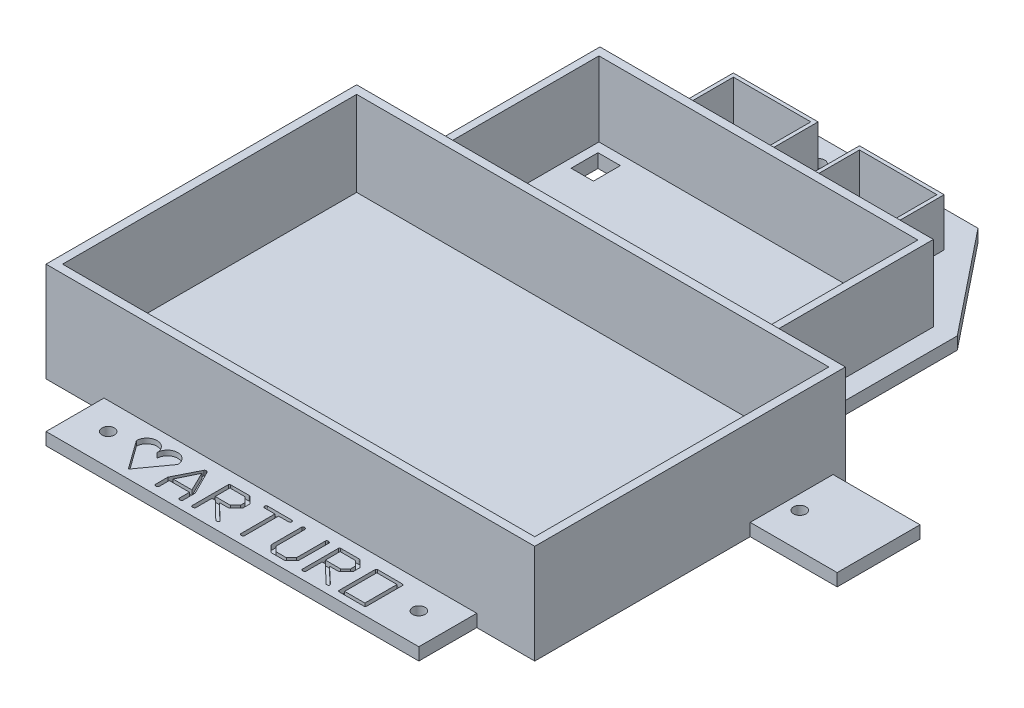
SolidWorks part; units mm, degrees
ref_plane "Front Plane" through (0, 0, 0) normal (0, 0, 1) x (1, 0, 0)
ref_plane "Top Plane" through (0, 0, 0) normal (0, 1, 0) x (1, 0, 0)
ref_plane "Right Plane" through (0, 0, 0) normal (1, 0, 0) x (0, 0, -1)
sketch "Sketch1" plane through (0, 0, 0) normal (0, 1, 0) x (1, 0, 0)
  line L1 (0, 0) -> (90, 0)
  line L2 (0, 0) -> (0, 145)
  line L3 (0, 145) -> (90, 145)
  line L4 (90, 0) -> (90, 145)
  dimension "D1" = 145
  dimension "D2" = 90
extrude "Boss-Extrude1" add sketch "Sketch1" along normal blind 3 contours L2 L3 L4 L1
sketch "Sketch3" plane through (0, 3, 0) normal (0, 1, 0) x (1, 0, 0)
  line L0 (90, 0) -> (90, 145) construction
  line L1 (90, 86) -> (125, 86)
  line L2 (90, 86) -> (90, 66)
  line L3 (90, 66) -> (125, 66)
  line L4 (125, 86) -> (125, 66)
  line L5 (0, 0) -> (90, 0) construction
  line L6 (0, 0) -> (0, 145) construction
  line L7 (0, 86) -> (-35, 86)
  line L8 (0, 86) -> (0, 66)
  line L9 (0, 66) -> (-35, 66)
  line L10 (-35, 86) -> (-35, 66)
  dimension "D1" = 66
extrude "Boss-Extrude2" add sketch "Sketch3" against normal blind 3
sketch "Sketch2" plane through (0, 3, 0) normal (0, 1, 0) x (1, 0, 0)
  circle A0 centre (7.5, 7.5) radius 1.5
  circle A1 centre (82.5, 7.5) radius 1.5
  dimension "D3" = 3
extrude "Cut-Extrude1" cut sketch "Sketch2" against normal blind 3
sketch "Sketch24" plane through (0, 3, 0) normal (0, 1, 0) x (1, 0, 0)
  line L0 (6.5, 51.5) -> (6.5, 15) construction
  line L2 (12.8, 9.003) -> (17.8, 2.0665)
  line L3 (17.8, 2.0665) -> (22.8, 9.003)
  line L4 (0, 0) -> (0, 66) construction
  arc A0 (17.8, 9.003) -> (12.8, 9.003) centre (15.3, 9.003) ccw
  arc A1 (22.8, 9.003) -> (17.8, 9.003) centre (20.3, 9.003) ccw
  text T0 "ARTURO" font "SWTxt" height in points 36
  dimension "D1" = 5
  dimension "D2" = 36.5
  dimension "D3" = 17.8
extrude "Cut-Extrude10" cut sketch "Sketch24" against normal blind 1.2
sketch "Sketch25" plane through (0, 3, 0) normal (0, 1, 0) x (1, 0, 0)
  circle A0 centre (-17.4688, 74.5) radius 1.5
  circle A1 centre (107.4688, 74.5) radius 1.5
extrude "Cut-Extrude11" cut sketch "Sketch25" against normal through all
sketch "Sketch27" plane through (0, 3, 0) normal (0, 1, 0) x (1, 0, 0)
  line L0 (0, 86) -> (0, 145) construction
  line L1 (4.75, 128.98) -> (85.25, 128.98)
  line L2 (4.75, 128.98) -> (4.75, 88.98)
  line L3 (4.75, 88.98) -> (85.25, 88.98)
  line L4 (85.25, 128.98) -> (85.25, 88.98)
  line L5 (125, 86) -> (90, 86) construction
  dimension "D1" = 80.5
  dimension "D2" = 40
  dimension "D3" = 4.75
  dimension "D4" = 2.98
extrude "Boss-Extrude4" add sketch "Sketch27" along normal blind 18.3
sketch "Sketch28" plane through (0, 21.3, 0) normal (0, 1, 0) x (1, 0, 0)
  line L0 (45, 128.98) -> (45, 88.98) construction
  line L1 (85.25, 128.98) -> (4.75, 128.98) construction
  line L2 (4.75, 88.98) -> (85.25, 88.98) construction
  line L3 (85.25, 88.98) -> (85.25, 128.98) construction
  line L4 (6.5, 90.98) -> (83.5, 90.98)
  line L5 (6.5, 90.98) -> (6.5, 126.98)
  line L6 (6.5, 126.98) -> (83.5, 126.98)
  line L7 (83.5, 90.98) -> (83.5, 126.98)
  line L8 (6.5, 90.98) -> (83.5, 126.98) construction
  line L9 (6.5, 126.98) -> (83.5, 90.98) construction
  point P6 (45, 108.98)
  dimension "D1" = 1.75
  dimension "D2" = 2
extrude "Cut-Extrude12" cut sketch "Sketch28" against normal blind 18
sketch "Sketch29" plane through (0, 3.3, 0) normal (0, 1, 0) x (1, 0, 0)
  line L1 (8.6295, 124.623) -> (14.0295, 124.623)
  line L2 (8.6295, 124.623) -> (8.6295, 118.123)
  line L3 (8.6295, 118.123) -> (14.0295, 118.123)
  line L4 (14.0295, 124.623) -> (14.0295, 118.123)
  dimension "D1" = 5.4
  dimension "D2" = 6.5
extrude "Cut-Extrude13" cut sketch "Sketch29" against normal blind 18
sketch "Sketch31" plane through (0, 3, 0) normal (0, 1, 0) x (1, 0, 0)
  line L1 (-14, 88.9845) -> (104, 88.9845)
  line L2 (-14, 88.9845) -> (-14, 13.9845)
  line L3 (-14, 13.9845) -> (104, 13.9845)
  line L4 (104, 88.9845) -> (104, 13.9845)
  line L5 (0, 0) -> (90, 0) construction
  point P8 (45, 0)
  point P9 (45, 13.9845)
  point P10 (0, 0)
  point P13 (0, 0)
  dimension "D1" = 118
  dimension "D2" = 75
extrude "Boss-Extrude5" add sketch "Sketch31" along normal mid plane 6
sketch "Sketch32" plane through (0, 6, 0) normal (0, 1, 0) x (1, 0, 0)
  line L1 (-14, 13.9845) -> (104, 13.9845)
  line L2 (-14, 13.9845) -> (-14, 88.9845)
  line L3 (-14, 88.9845) -> (104, 88.9845)
  line L4 (104, 13.9845) -> (104, 88.9845)
extrude "Boss-Extrude6" add sketch "Sketch32" along normal blind 18
sketch "Sketch33" plane through (0, 24, 0) normal (0, 1, 0) x (1, 0, 0)
  line L0 (45, 88.9845) -> (45, 13.9845) construction
  line L8 (104, 88.9845) -> (-14, 88.9845) construction
  line L9 (-14, 13.9845) -> (104, 13.9845) construction
  line L13 (-14, 88.9845) -> (-14, 13.9845) construction
  line L14 (-12, 86.9845) -> (102, 86.9845)
  line L15 (-12, 86.9845) -> (-12, 15.9845)
  line L16 (-12, 15.9845) -> (102, 15.9845)
  line L17 (102, 86.9845) -> (102, 15.9845)
  line L18 (-12, 86.9845) -> (102, 15.9845) construction
  line L19 (-12, 15.9845) -> (102, 86.9845) construction
  point P6 (45.9049, 51)
  point P7 (45, 51.4845)
  dimension "D1" = 2
  dimension "D2" = 2
extrude "Cut-Extrude14" cut sketch "Sketch33" against normal mid plane 41
sketch "Sketch34" plane through (0, 0, -145) normal (0, 0, -1) x (-1, 0, 0)
  line L1 (0, 3) -> (-90, 3)
  line L2 (0, 3) -> (0, 0)
  line L3 (0, 0) -> (-90, 0)
  line L4 (-90, 3) -> (-90, 0)
extrude "Boss-Extrude7" add sketch "Sketch34" along normal blind 10
sketch "Sketch35" plane through (0, 3, 0) normal (0, 1, 0) x (1, 0, 0)
  line L0 (45, 155) -> (45, 131.8524) construction
  line L1 (19.55, 131.6348) -> (40, 131.6348)
  line L2 (19.55, 131.6348) -> (19.55, 146.3848)
  line L3 (19.55, 146.3848) -> (40, 146.3848)
  line L4 (40, 131.6348) -> (40, 146.3848)
  line L5 (50, 131.6348) -> (70.45, 131.6348)
  line L6 (50, 131.6348) -> (50, 146.3848)
  line L7 (50, 146.3848) -> (70.45, 146.3848)
  line L8 (70.45, 131.6348) -> (70.45, 146.3848)
  line L9 (0, 155) -> (90, 155) construction
  point P12 (40, 139.0098)
  dimension "D1" = 20.45
  dimension "D2" = 14.75
  dimension "D3" = 20.45
  dimension "D4" = 5
  dimension "D5" = 5
  dimension "D6" = 14.75
extrude "Boss-Extrude8" add sketch "Sketch35" along normal blind 11.55
sketch "Sketch36" plane through (0, 14.55, 0) normal (0, 1, 0) x (1, 0, 0)
  line L0 (60.225, 146.3848) -> (60.225, 131.6348) construction
  line L1 (70.45, 146.3848) -> (50, 146.3848) construction
  line L2 (50, 131.6348) -> (70.45, 131.6348) construction
  line L3 (29.775, 146.3848) -> (29.775, 131.6348) construction
  line L4 (40, 146.3848) -> (19.55, 146.3848) construction
  line L5 (19.55, 131.6348) -> (40, 131.6348) construction
  line L7 (20.425, 132.5098) -> (39.125, 132.5098)
  line L8 (20.425, 132.5098) -> (20.425, 145.5098)
  line L9 (20.425, 145.5098) -> (39.125, 145.5098)
  line L10 (39.125, 132.5098) -> (39.125, 145.5098)
  line L11 (20.425, 132.5098) -> (39.125, 145.5098) construction
  line L12 (20.425, 145.5098) -> (39.125, 132.5098) construction
  line L13 (50.875, 132.5098) -> (69.575, 132.5098)
  line L14 (50.875, 132.5098) -> (50.875, 145.5098)
  line L15 (50.875, 145.5098) -> (69.575, 145.5098)
  line L16 (69.575, 132.5098) -> (69.575, 145.5098)
  line L17 (50.875, 132.5098) -> (69.575, 145.5098) construction
  line L18 (50.875, 145.5098) -> (69.575, 132.5098) construction
  point P12 (29.775, 139.0098)
  point P17 (60.225, 139.0098)
  dimension "D1" = 18.7
  dimension "D2" = 18.7
  dimension "D3" = 13
  dimension "D4" = 13
extrude "Cut-Extrude15" cut sketch "Sketch36" against normal blind 11.55
sketch "Sketch37" plane through (0, 3, 0) normal (0, 1, 0) x (1, 0, 0)
  line L0 (28.925, 134.7598) -> (38.625, 134.7598)
  line L1 (38.625, 134.7598) -> (38.625, 143.2598)
  line L2 (38.625, 143.2598) -> (28.925, 143.2598)
  line L5 (39.125, 132.5098) -> (39.125, 145.5098) construction
  line L6 (39.125, 139.0098) -> (38.625, 139.0098) construction
  line L7 (59.375, 134.7598) -> (69.075, 134.7598)
  line L8 (69.075, 134.7598) -> (69.075, 143.2598)
  line L9 (69.075, 143.2598) -> (59.375, 143.2598)
  line L10 (69.575, 139.0098) -> (69.075, 139.0098) construction
  line L11 (69.575, 132.5098) -> (69.575, 145.5098) construction
  arc A0 (28.925, 134.7598) -> (28.925, 143.2598) centre (28.925, 139.0098) cw
  arc A1 (59.375, 134.7598) -> (59.375, 143.2598) centre (59.375, 139.0098) cw
  point P9 (38.625, 139.0098)
  point P18 (69.075, 139.0098)
  dimension "D1" = 9.7
  dimension "D5" = 0.5
  dimension "D2" = 9.7
  dimension "D3" = 8.5
  dimension "D4" = 8.5
  dimension "D6" = 0.5
extrude "Cut-Extrude16" cut sketch "Sketch37" against normal blind 11.55
sketch "Sketch38" plane through (0, 3, 0) normal (0, 1, 0) x (1, 0, 0)
  line L0 (20, 155) -> (0, 130)
  line L1 (0, 155) -> (90, 155) construction
  line L2 (0, 88.9845) -> (0, 155) construction
  line L3 (0, 130) -> (0, 155)
  line L4 (0, 155) -> (20, 155)
  line L5 (70, 155) -> (90, 130)
  line L6 (90, 88.9845) -> (90, 155) construction
  line L7 (90, 130) -> (90, 155)
  line L8 (90, 155) -> (70, 155)
  dimension "D1" = 20
  dimension "D2" = 25
  dimension "D3" = 20
  dimension "D4" = 25
extrude "Cut-Extrude17" cut sketch "Sketch38" against normal blind 11.55
sketch "Sketch39" plane through (0, 3, 0) normal (0, 1, 0) x (1, 0, 0)
  circle A0 centre (37.25, 149.2558) radius 1.5
  circle A1 centre (52.75, 149.2558) radius 1.5
  dimension "D1" = 3
  dimension "D2" = 15.5
extrude "Cut-Extrude19" cut sketch "Sketch39" against normal blind 10
